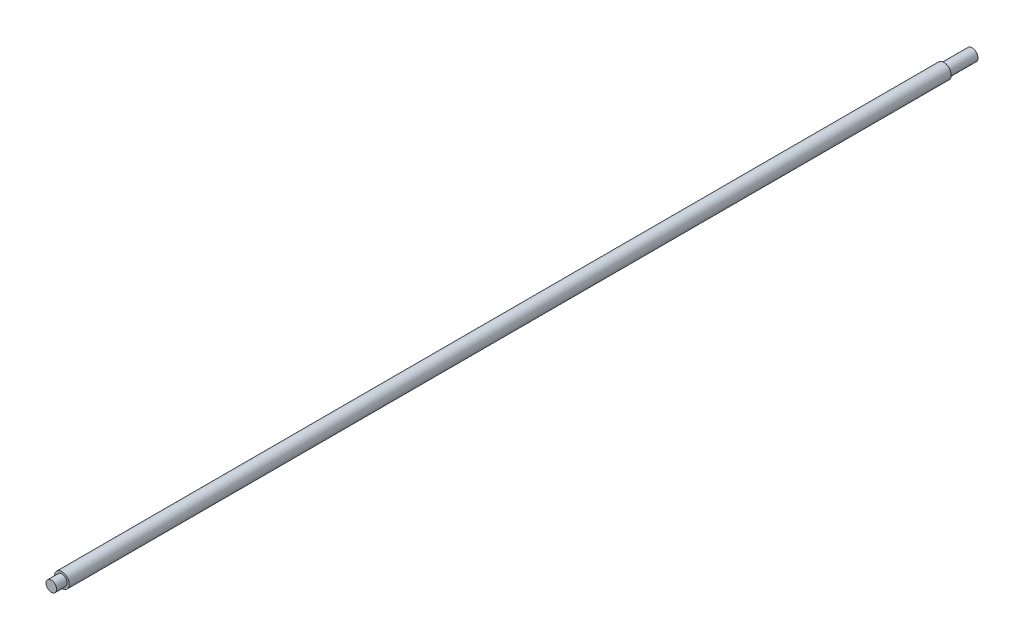
SolidWorks part; units mm, degrees
ref_plane "Płaszczyzna przednia" through (0, 0, 0) normal (0, 0, 1) x (1, 0, 0)
ref_plane "Płaszczyzna górna" through (0, 0, 0) normal (0, 1, 0) x (1, 0, 0)
ref_plane "Płaszczyzna prawa" through (0, 0, 0) normal (1, 0, 0) x (0, 0, -1)
sketch "Szkic2" plane through (0, 0, 0) normal (0, 0, 1) x (1, 0, 0)
  circle A0 centre (0, 0) radius 12.5
extrude "Dodanie-wyciągnięcie1" add sketch "Szkic2" along normal blind 1497
sketch "Szkic3" plane through (0, 0, 1497) normal (0, 0, 1) x (1, 0, 0)
  circle A0 centre (0, 0) radius 9
  dimension "D1" = 18
extrude "Dodanie-wyciągnięcie2" add sketch "Szkic3" along normal blind 18
sketch "Szkic4" plane through (0, 0, 0) normal (0, 0, -1) x (-1, 0, 0)
  circle A0 centre (0, 0) radius 10
extrude "Dodanie-wyciągnięcie3" add sketch "Szkic4" along normal blind 48
